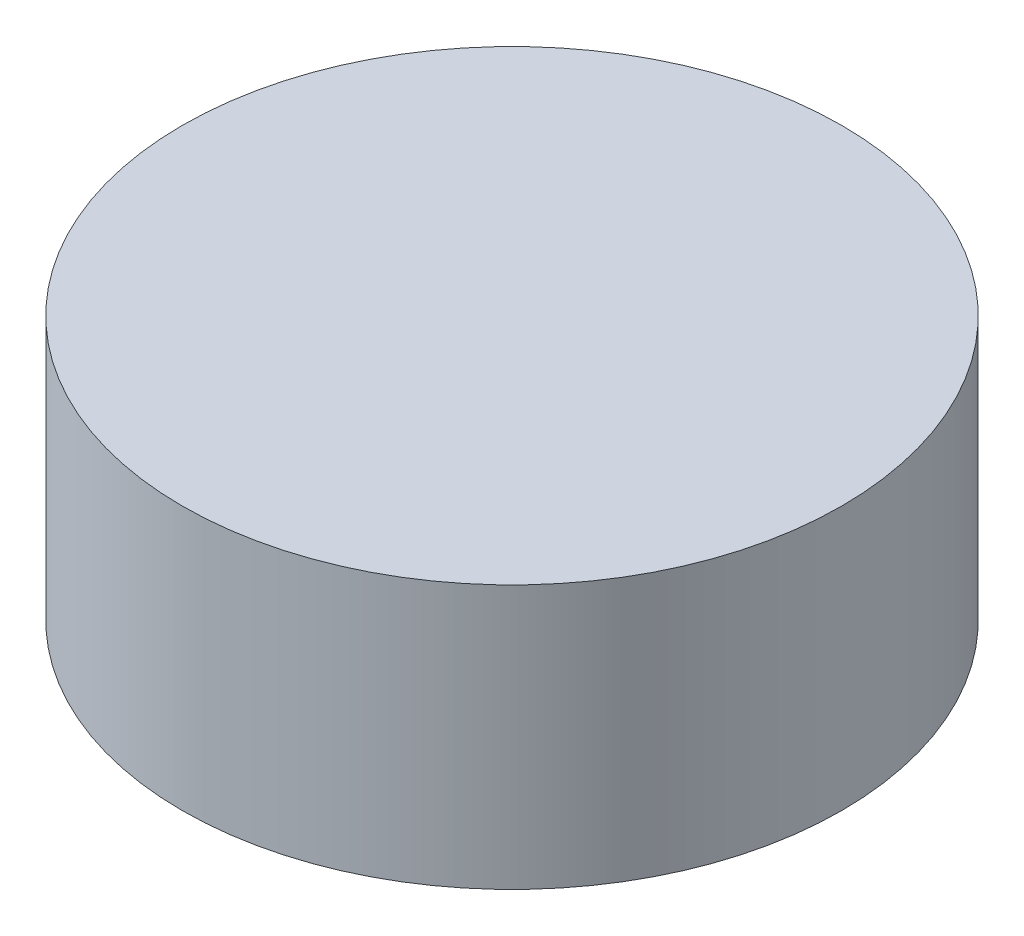
SolidWorks part; units mm, degrees
ref_plane "Front Plane" through (0, 0, 0) normal (0, 0, 1) x (1, 0, 0)
ref_plane "Top Plane" through (0, 0, 0) normal (0, 1, 0) x (1, 0, 0)
ref_plane "Right Plane" through (0, 0, 0) normal (1, 0, 0) x (0, 0, -1)
sketch "Sketch1" plane through (0, 0, 0) normal (0, 1, 0) x (1, 0, 0)
  circle A0 centre (0, 0) radius 2.5
  dimension "D1" = 5
extrude "Boss-Extrude1" add sketch "Sketch1" along normal blind 2
